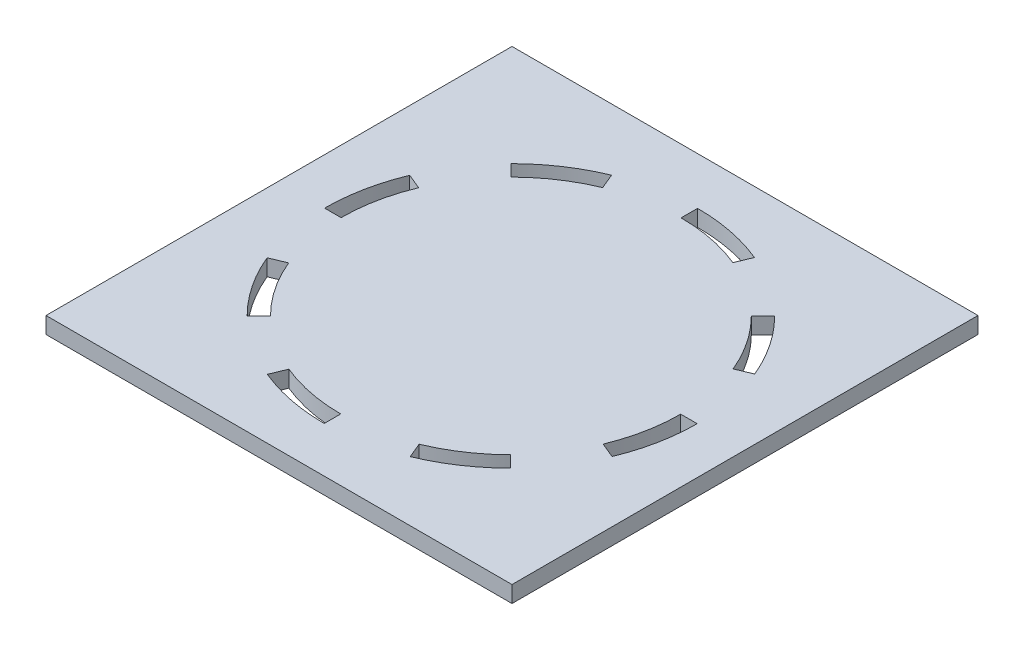
SolidWorks part; units mm, degrees
ref_plane "Front Plane" through (0, 0, 0) normal (0, 0, 1) x (1, 0, 0)
ref_plane "Top Plane" through (0, 0, 0) normal (0, 1, 0) x (1, 0, 0)
ref_plane "Right Plane" through (0, 0, 0) normal (1, 0, 0) x (0, 0, -1)
sketch "Sketch1" plane through (0, 0, 0) normal (0, 1, 0) x (1, 0, 0)
  line L1 (0, 0) -> (143.51, 0)
  line L2 (0, 0) -> (0, 143.51)
  line L3 (0, 143.51) -> (143.51, 143.51)
  line L4 (143.51, 0) -> (143.51, 143.51)
  dimension "D1" = 143.51
  dimension "D2" = 143.51
extrude "Boss-Extrude1" add sketch "Sketch1" along normal blind 5.08
sketch "Sketch3" plane through (0, 5.08, 0) normal (0, 1, 0) x (1, 0, 0)
  line L0 (71.755, 143.51) -> (71.755, 0) construction
  line L1 (143.51, 143.51) -> (0, 143.51) construction
  line L2 (0, 0) -> (143.51, 0) construction
  line L3 (0, 71.755) -> (143.51, 71.755) construction
  line L4 (0, 143.51) -> (0, 0) construction
  line L5 (143.51, 0) -> (143.51, 143.51) construction
  line L6 (71.755, 128.905) -> (71.755, 123.825)
  line L7 (93.6254, 124.5547) -> (91.6813, 119.8614)
  arc A0 (71.755, 128.905) -> (93.6254, 124.5547) centre (71.755, 71.755) cw
  arc A1 (71.755, 123.825) -> (91.6813, 119.8614) centre (71.755, 71.755) cw
  point P17 (0, 0)
  point P18 (0, 0)
  dimension "D1" = 5.08
  dimension "D2" = 57.15
extrude "Cut-Extrude1" cut sketch "Sketch3" against normal through all
pattern_circular "CirPattern1" count 8 over 360 about axis through (71.6987, 0, -71.4718) along (0, 1, 0) of "Cut-Extrude1"
equation "\"GMaterial\" = 0.21in"
equation "\"MDF\"= 0.21in"
equation "\"Foamcore\"= 0.2in"
equation "\"D1@Sketch1\"=2*\"Foamcore\"+5.25"
equation "\"D2@Sketch1\"=2*\"Foamcore\"+5.25"
equation "\"D1@Boss-Extrude1\"=\"Foamcore\""
equation "\"D1@Sketch3\"=\"Foamcore\""
